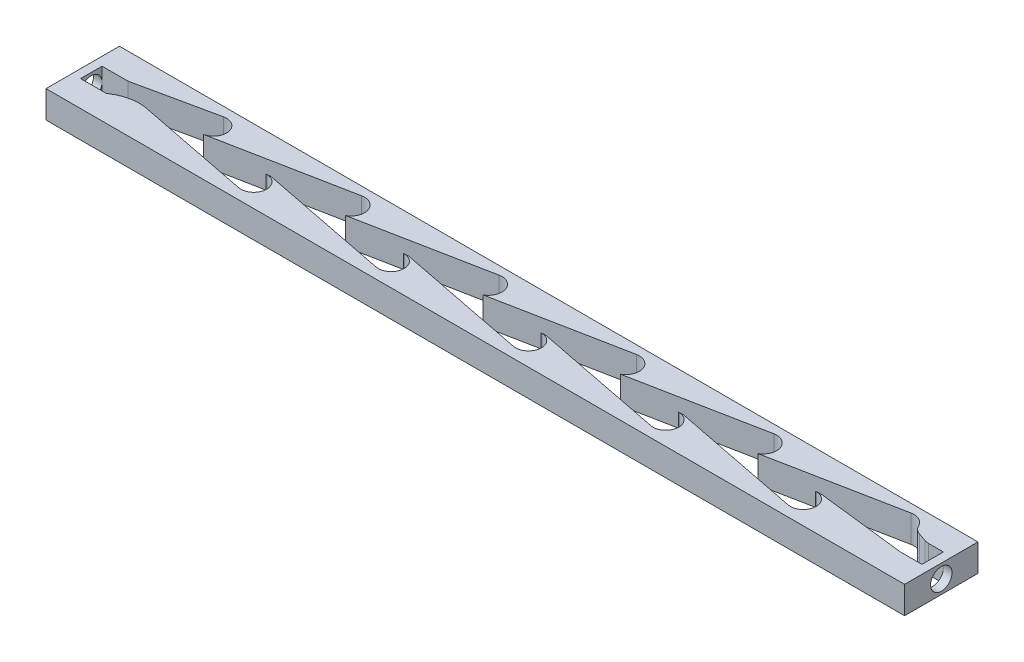
SolidWorks part; units mm, degrees
ref_plane "Front Plane" through (0, 0, 0) normal (0, 0, 1) x (1, 0, 0)
ref_plane "Top Plane" through (0, 0, 0) normal (0, 1, 0) x (1, 0, 0)
ref_plane "Right Plane" through (0, 0, 0) normal (1, 0, 0) x (0, 0, -1)
sketch "Sketch1" plane through (0, 0, 0) normal (0, 1, 0) x (1, 0, 0)
  line L1 (0, 0) -> (200, 0)
  line L2 (0, 0) -> (0, 17.1)
  line L3 (0, 17.1) -> (200, 17.1)
  line L4 (200, 0) -> (200, 17.1)
  dimension "D1" = 17.1
  dimension "D2" = 200
extrude "Boss-Extrude1" add sketch "Sketch1" along normal blind 6.35
sketch "Sketch2" plane through (0, 6.35, 0) normal (0, 1, 0) x (1, 0, 0)
  line L0 (0, 8.55) -> (200, 8.55) construction
  line L1 (0, 17.1) -> (0, 0) construction
  line L2 (200, 0) -> (200, 17.1) construction
  line L3 (0, 12.05) -> (200, 12.05) construction
  line L4 (2, 11.05) -> (8, 11.05)
  line L5 (2, 6.05) -> (8, 6.05)
  line L6 (2, 11.05) -> (2, 6.05)
  line L7 (27, 17.1) -> (27, 0) construction
  line L8 (200, 17.1) -> (0, 17.1) construction
  line L9 (0, 0) -> (200, 0) construction
  line L10 (8, 11.05) -> (26.3719, 14.9835)
  line L11 (8, 6.05) -> (11.75, 8.5)
  line L12 (11.75, 8.5) -> (27.6057, 9.1118)
  arc A0 (26.3719, 14.9835) -> (27.6057, 9.1118) centre (27, 12.05) cw
  dimension "D5" = 3
  dimension "D1" = 3.5
  dimension "D2" = 5
  dimension "D3" = 6
  dimension "D4" = 27
  dimension "D7" = 8.5
extrude "Cut-Extrude1" cut sketch "Sketch2" against normal up to next
sketch "Sketch3" plane through (0, 6.35, 0) normal (0, 1, 0) x (1, 0, 0)
  line L0 (43, 17.1) -> (43, 0) construction
  line L1 (200, 17.1) -> (0, 17.1) construction
  line L2 (0, 0) -> (200, 0) construction
  line L3 (27, 0) -> (27, 17.1) construction
  line L4 (0, 17.1) -> (0, 0) construction
  line L5 (0, 5.4) -> (200, 5.4) construction
  line L6 (200, 0) -> (200, 17.1) construction
  line L7 (42.42, 2.4566) -> (11.75, 8.5)
  line L8 (43.1379, 8.3968) -> (27.6057, 9.1118)
  line L9 (11.75, 8.5) -> (27.6057, 9.1118)
  line L10 (200, 8.55) -> (0, 8.55) construction
  arc A0 (43.1379, 8.3968) -> (42.42, 2.4566) centre (43, 5.4) cw
  dimension "D3" = 3
  dimension "D1" = 27
  dimension "D2" = 16
  dimension "D4" = 3.15
extrude "Cut-Extrude2" cut sketch "Sketch3" against normal up to next (6.35 mm away)
pattern_linear "LPattern1" count 5 spacing 32 along (1, 0, 0) of "Cut-Extrude2"
sketch "Sketch4" plane through (0, 6.35, 0) normal (0, 1, 0) x (1, 0, 0)
  line L0 (59, 17.1) -> (59, 0) construction
  line L1 (200, 17.1) -> (0, 17.1) construction
  line L2 (0, 0) -> (200, 0) construction
  line L3 (0, 17.1) -> (0, 0) construction
  line L4 (0, 12.05) -> (200, 12.05) construction
  line L5 (200, 0) -> (200, 17.1) construction
  line L6 (200, 12.05) -> (200, 8.55) construction
  line L7 (200, 8.55) -> (0, 8.55) construction
  line L8 (27.6057, 9.1118) -> (58.3946, 15.1413)
  line L9 (42.8782, 8.4088) -> (59.0957, 8.9015)
  line L10 (42.8782, 8.4088) -> (27.6057, 9.1118)
  line L11 (43.1379, 8.3968) -> (27.6057, 9.1118) construction
  arc A0 (59.0957, 8.9015) -> (58.3946, 15.1413) centre (59, 12.05) ccw
  dimension "D3" = 3.15
  dimension "D1" = 59
  dimension "D2" = 3.5
extrude "Cut-Extrude3" cut sketch "Sketch4" against normal up to next (6.35 mm away)
pattern_linear "LPattern2" count 5 spacing 32 along (1, 0, 0) of "Cut-Extrude3"
fillet "Fillet1" radius 10 1 edges at (11.75, 3.175, -8.5)
sketch "Sketch5" plane through (0, 6.35, 0) normal (0, 1, 0) x (1, 0, 0)
  line L0 (200, 8.55) -> (198, 8.55) construction
  line L1 (198, 6.05) -> (193, 6.05)
  line L2 (200, 0) -> (200, 17.1) construction
  line L3 (198, 11.05) -> (198, 6.05)
  line L4 (193, 6.05) -> (172.3484, 8.4534)
  line L5 (170.8782, 8.4088) -> (187.0957, 8.9015) construction
  line L6 (190.1303, 12.4017) -> (194, 11.05)
  line L7 (190.1303, 12.4017) -> (172.3484, 8.4534)
  line L9 (198, 11.05) -> (194, 11.05)
  arc A0 (187.0957, 8.9015) -> (186.3946, 15.1413) centre (187, 12.05) ccw construction
  dimension "D1" = 5
  dimension "D2" = 2
  dimension "D3" = 5
extrude "Cut-Extrude6" cut sketch "Sketch5" against normal up to next
fillet "Fillet2" radius 3 2 edges at (190.1303, 3.175, -12.4017) (194, 3.175, -11.05)
sketch "Sketch6" plane through (200, 0, 0) normal (1, 0, 0) x (0, 0, -1)
  line L0 (0, 6.35) -> (17.1, 0) construction
  circle A0 centre (8.55, 3.175) radius 2.5
  dimension "D1" = 5
extrude "Cut-Extrude7" cut sketch "Sketch6" against normal up to next
sketch "Sketch7" plane through (0, 0, 0) normal (-1, 0, 0) x (0, 0, 1)
  line L0 (-17.1, 6.35) -> (0, 0) construction
  circle A0 centre (-8.55, 3.175) radius 2.5
  dimension "D1" = 5
extrude "Cut-Extrude8" cut sketch "Sketch7" against normal up to next
